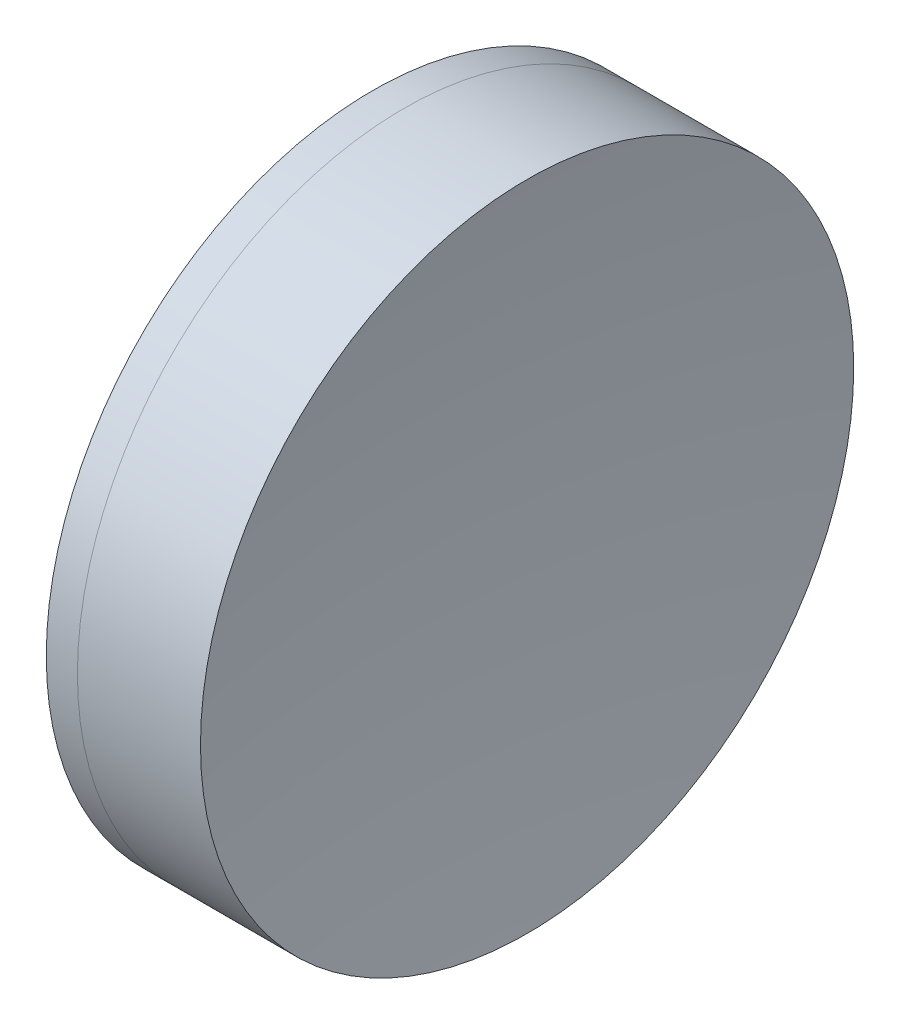
SolidWorks part; units mm, degrees
ref_plane "前视基准面" through (0, 0, 0) normal (0, 0, 1) x (1, 0, 0)
ref_plane "上视基准面" through (0, 0, 0) normal (0, 1, 0) x (1, 0, 0)
ref_plane "右视基准面" through (0, 0, 0) normal (1, 0, 0) x (0, 0, -1)
sketch "草图1" plane through (0, 0, 0) normal (0, 1, 0) x (1, 0, 0)
  line L0 (-0.8161, 0) -> (118.0272, 0) construction
  line L1 (57.7791, -12.7) -> (58.9886, -12.7)
  line L2 (57.7791, 12.7) -> (58.9886, 12.7)
  arc A0 (58.9886, -12.7) -> (58.9886, 12.7) centre (2.7242, 0) ccw
  arc A1 (57.7791, 12.7) -> (57.7791, -12.7) centre (99.8542, 0) ccw
  point P10 (55.9042, 0)
  point P11 (60.4042, 0)
  dimension "D3" = 43.95
  dimension "D4" = 57.68
  dimension "D1" = 12.7
  dimension "D2" = 12.7
  dimension "D5" = 4.5
revolve "旋转1" add sketch "草图1" angle 360 about L0
sketch "草图2" plane through (0, 0, 0) normal (0, 1, 0) x (1, 0, 0)
  line L0 (-0.5519, 0) -> (162.8134, 0) construction
  line L2 (58.9886, 12.7) -> (63.7744, 12.7)
  line L3 (58.9886, -12.7) -> (63.7744, -12.7)
  arc A0 (63.7744, 12.7) -> (63.7744, -12.7) centre (156.0142, 0) ccw
  arc A1 (58.9886, -12.7) -> (58.9886, 12.7) centre (2.7242, 0) ccw construction
  arc A2 (58.9886, -12.7) -> (58.9886, 12.7) centre (2.7242, 0) ccw
  point P4 (60.4042, 0)
  point P8 (62.9042, 0)
  dimension "D1" = 93.11
  dimension "D2" = 2.5
revolve "旋转2" add sketch "草图2" angle 360 about L0
